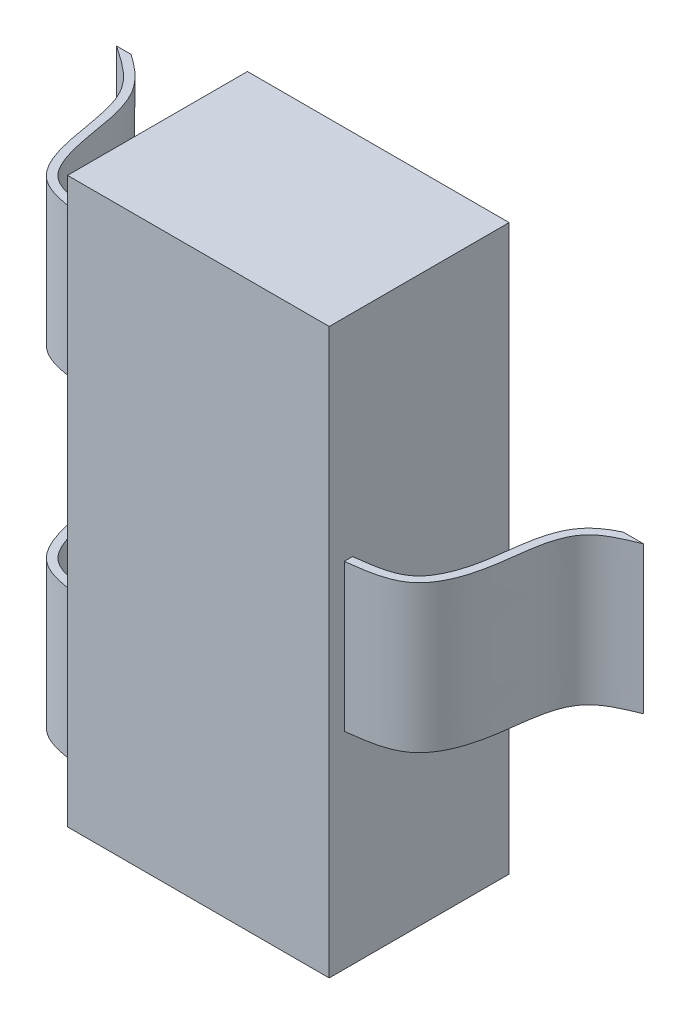
SolidWorks part; units mm, degrees
ref_plane "Front" through (0, 0, 0) normal (0, 0, 1) x (1, 0, 0)
ref_plane "Top" through (0, 0, 0) normal (0, 1, 0) x (1, 0, 0)
ref_plane "Right" through (0, 0, 0) normal (1, 0, 0) x (0, 0, -1)
sketch "COMPONENT_OUTLINE" plane through (0, 0, 0) normal (0, 0, 1) x (1, 0, 0)
  line L0 (-0.875, -1.71) -> (0.725, -1.71)
  line L1 (0.725, -1.71) -> (0.725, -0.45)
  line L2 (0.725, -0.45) -> (1.5475, -0.45)
  line L3 (1.5475, -0.45) -> (1.5475, 0.45)
  line L4 (1.5475, 0.45) -> (0.725, 0.45)
  line L5 (0.725, 0.45) -> (0.725, 1.74)
  line L6 (0.725, 1.74) -> (-0.875, 1.74)
  line L7 (-0.875, 1.74) -> (-0.875, 1.475)
  line L8 (-0.875, 1.475) -> (-1.675, 1.475)
  line L9 (-1.675, 1.475) -> (-1.675, 0.575)
  line L10 (-1.675, 0.575) -> (-0.875, 0.575)
  line L11 (-0.875, 0.575) -> (-0.875, -0.55)
  line L12 (-0.875, -0.55) -> (-1.675, -0.55)
  line L13 (-1.675, -0.55) -> (-1.675, -1.45)
  line L14 (-1.675, -1.45) -> (-0.875, -1.45)
  line L15 (-0.875, -1.45) -> (-0.875, -1.71)
extrude "Extrude1" add sketch "COMPONENT_OUTLINE" along normal blind 1.1
sketch "Sketch1" plane through (0, -1.45, 0) normal (0, -1, 0) x (1, 0, 0)
  line L0 (0.725, 1.1) -> (0.725, 0) construction
  line L1 (0.725, 1.1) -> (1.5475, 1.1) construction
  line L2 (0.725, 1.1) -> (1.5475, 1.1)
  line L3 (0.725, 1.1) -> (0.725, 1.0077)
  line L4 (0.725, 0) -> (1.5475, 0)
  line L5 (1.5475, 0) -> (1.5475, 1.1)
  line L6 (1.5475, 1.1) -> (0.725, 1.1)
  line L7 (0.725, 1.1) -> (0.725, 0)
  line L8 (-1.675, 0) -> (-0.875, 0)
  line L9 (1.5475, 0) -> (1.5475, 1.1)
  line L10 (-0.875, 1.1) -> (-0.875, 0) construction
  line L11 (-0.875, 0) -> (-0.875, 1.1)
  line L12 (-0.875, 1.1) -> (-1.675, 1.1)
  line L13 (-1.675, 1.1) -> (-1.675, 0)
  line L15 (-1.675, 1.1) -> (-0.875, 1.1) construction
  line L16 (-0.875, 1.1) -> (-0.875, 1.0077)
  line L17 (-1.675, 1.1) -> (-1.675, 0)
  line L18 (-1.675, 1.1) -> (-0.875, 1.1)
  spline S0 degree 3 poles (0.725, 1.0077) (0.8413, 0.9932) (1.0744, 0.9643) (1.2407, 0.5663) (1.2121, 0.1368) (1.4664, 0.0331) (1.5475, 0) knots 0 0 0 0 0.228896 0.459105 0.827412 1 1 1 1
  spline S1 degree 3 poles (-0.875, 1.0077) (-0.9925, 0.9937) (-1.2471, 0.9635) (-1.3424, 0.5619) (-1.3845, 0.1964) (-1.5847, 0.061) (-1.675, 0) knots 0 0 0 0 0.232825 0.504412 0.776556 1 1 1 1
  dimension "D1" = 0
  dimension "D2" = 0
extrude "Cut-Extrude1" cut sketch "Sketch1" against normal through all
sketch "Sketch2" plane through (0, -1.45, 0) normal (0, -1, 0) x (1, 0, 0)
  line L0 (0.725, 0) -> (1.5475, 0) construction
  line L1 (-1.675, 0) -> (-0.875, 0) construction
  line L2 (-0.875, 1.1) -> (-0.875, 0) construction
  line L3 (0.725, 1.1) -> (0.725, 0) construction
  line L4 (0.725, 0) -> (1.4216, 0)
  line L5 (-1.5864, 0) -> (-0.875, 0)
  line L6 (-0.875, 0.9573) -> (-0.875, 0)
  line L7 (0.725, 0.9573) -> (0.725, 0)
  spline S4 degree 3 poles (-1399.6739, -1427.1086) (27.5464, 26.6744) (4.2082, -1.8354) (1.3274, 0.0555) (1.3019, 0.0766) (1.2599, 0.1255) (1.2434, 0.1526) (1.1776, 0.2949) (1.1743, 0.4297) (1.1341, 0.6802) (1.0936, 0.7982) (0.9922, 0.8938) (0.9496, 0.9136) (-2.3582, 1.8099) (-37.5636, -21.8955) (1376.2748, 1452.6995) knots -6.47383 -6.47383 -6.47383 -6.47383 0.125 0.125 0.1875 0.1875 0.25 0.25 0.5 0.5 0.75 0.75 0.875 0.875 8.558622 8.558622 8.558622 8.558622 only from (1.5286, -0.0463) to (0.7188, 0.9581)
  spline S5 degree 3 poles (1.4216, 0) (1.3984, 0.0113) (1.3758, 0.0236) (1.3274, 0.0555) (1.3019, 0.0766) (1.2599, 0.1255) (1.2434, 0.1526) (1.1776, 0.2949) (1.1743, 0.4297) (1.1341, 0.6802) (1.0936, 0.7982) (0.9922, 0.8938) (0.9496, 0.9136) (0.8454, 0.9419) (0.7863, 0.9497) (0.725, 0.9573) knots 0.075414 0.075414 0.075414 0.075414 0.125 0.125 0.1875 0.1875 0.25 0.25 0.5 0.5 0.75 0.75 0.875 0.875 0.995949 0.995949 0.995949 0.995949
  spline S7 degree 3 poles (1632.1571, -1153.5193) (-27.576, 17.0305) (-4.577, -2.5522) (-1.45, 0.1082) (-1.407, 0.1552) (-1.3178, 0.318) (-1.3049, 0.443) (-1.2606, 0.6877) (-1.228, 0.8064) (-1.1372, 0.8965) (-1.0968, 0.9155) (2.0899, 1.7638) (39.0835, -20.5145) (-1488.7019, 1337.4417) knots -8.017661 -8.017661 -8.017661 -8.017661 0.125 0.125 0.25 0.25 0.5 0.5 0.75 0.75 0.875 0.875 8.439096 8.439096 8.439096 8.439096 only from (-1.647, -0.0414) to (-0.8691, 0.958)
  spline S8 degree 3 poles (-1.5864, 0) (-1.5559, 0.0214) (-1.5257, 0.0437) (-1.45, 0.1082) (-1.407, 0.1552) (-1.3178, 0.318) (-1.3049, 0.443) (-1.2606, 0.6877) (-1.228, 0.8064) (-1.1372, 0.8965) (-1.0968, 0.9155) (-0.9949, 0.9426) (-0.936, 0.9501) (-0.875, 0.9573) knots 0.049723 0.049723 0.049723 0.049723 0.125 0.125 0.25 0.25 0.5 0.5 0.75 0.75 0.875 0.875 0.996097 0.996097 0.996097 0.996097
  dimension "D1" = 0.05
  dimension "D2" = 0.05
extrude "Cut-Extrude2" cut sketch "Sketch2" against normal through all
